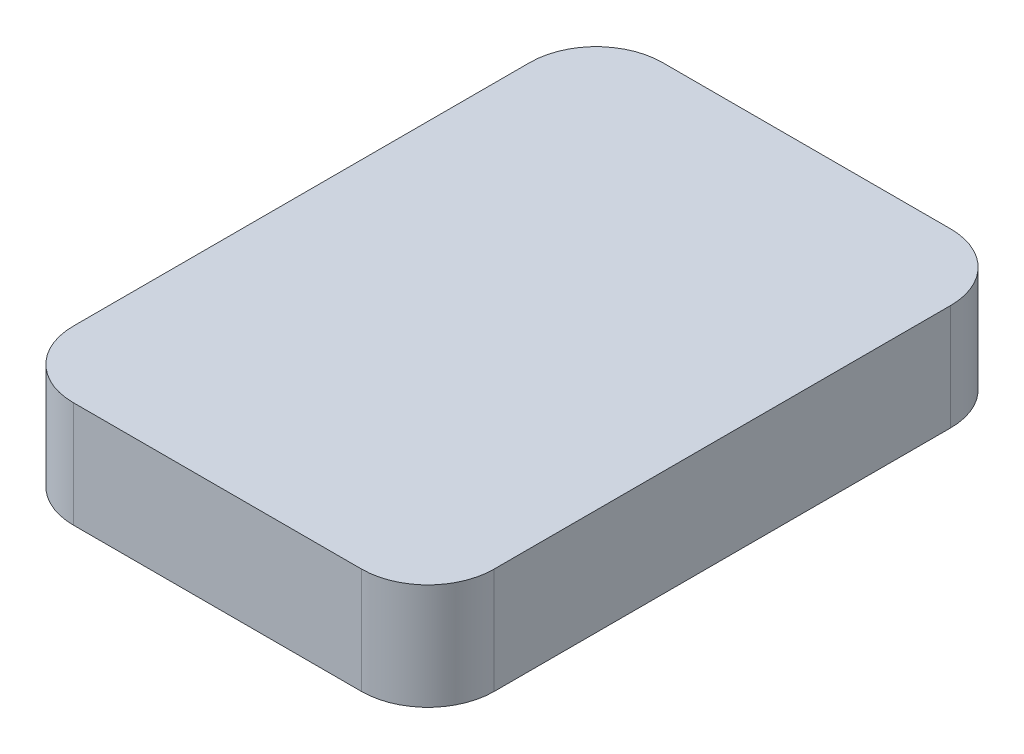
SolidWorks part; units mm, degrees
ref_plane "Front Plane" through (0, 0, 0) normal (0, 0, 1) x (1, 0, 0)
ref_plane "Top Plane" through (0, 0, 0) normal (0, 1, 0) x (1, 0, 0)
ref_plane "Right Plane" through (0, 0, 0) normal (1, 0, 0) x (0, 0, -1)
sketch "Sketch1" plane through (0, 0, 0) normal (0, 1, 0) x (1, 0, 0)
  line L1 (-31.75, -44.45) -> (31.75, -44.45)
  line L2 (-31.75, -44.45) -> (-31.75, 44.45)
  line L3 (-31.75, 44.45) -> (31.75, 44.45)
  line L4 (31.75, -44.45) -> (31.75, 44.45)
  line L5 (-31.75, -44.45) -> (31.75, 44.45) construction
  line L6 (-31.75, 44.45) -> (31.75, -44.45) construction
  point P0 (0, 0)
  dimension "D1" = 63.5
  dimension "D2" = 88.9
extrude "Boss-Extrude1" add sketch "Sketch1" along normal blind 16
fillet "Fillet1" radius 10 4 edges at (31.75, 8, 44.45) (31.75, 8, -44.45) (-31.75, 8, -44.45) (-31.75, 8, 44.45)
sketch "Sketch2" plane through (0, 16, 0) normal (0, 1, 0) x (1, 0, 0)
  line L0 (-221.0507, 48.5129) -> (389.6025, 98.866) construction
  line L1 (55.4761, 180.0009) -> (662.1427, 180.0009) construction
  line L2 (19.8291, 170.6934) -> (224.4958, 170.6934) construction
